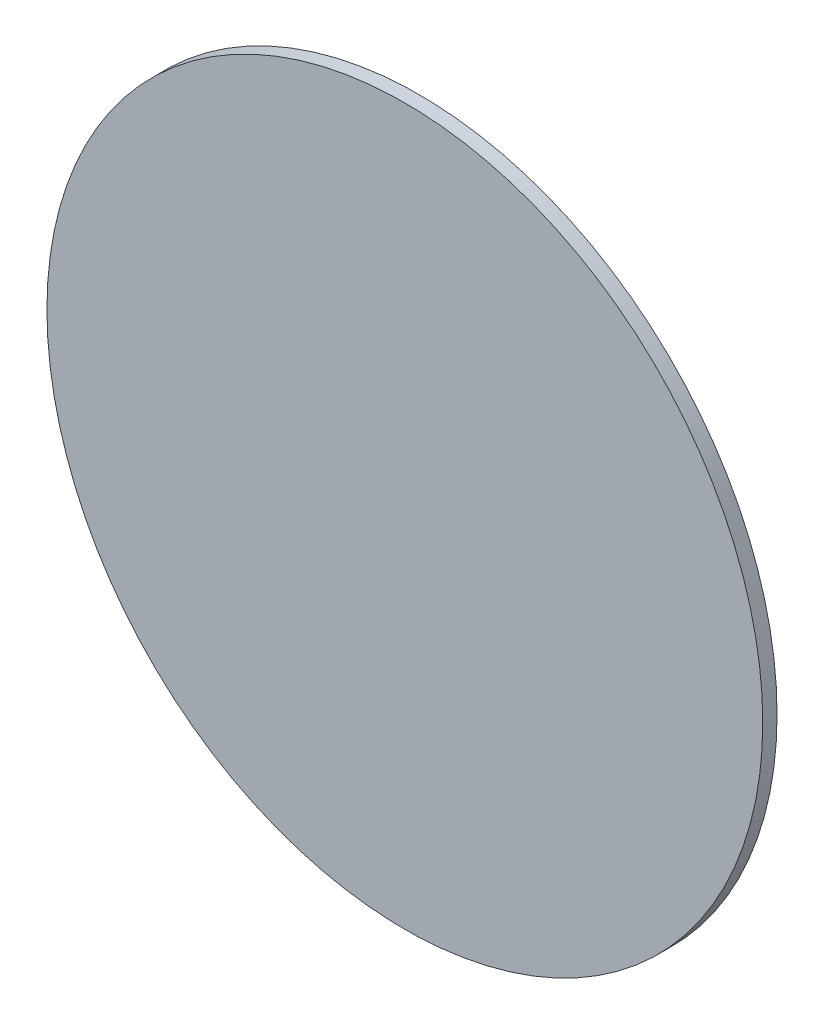
SolidWorks part; units mm, degrees
material "Glass"
ref_plane "Front Plane" through (0, 0, 0) normal (0, 0, 1) x (1, 0, 0)
ref_plane "Top Plane" through (0, 0, 0) normal (0, 1, 0) x (1, 0, 0)
ref_plane "Right Plane" through (0, 0, 0) normal (1, 0, 0) x (0, 0, -1)
sketch "Sketch1" plane through (0, 0, 0) normal (0, 0, 1) x (1, 0, 0)
  circle A0 centre (0, 0) radius 6.35
  dimension "D1" = 12.7
extrude "Boss-Extrude1" add sketch "Sketch1" along normal blind 0.254
